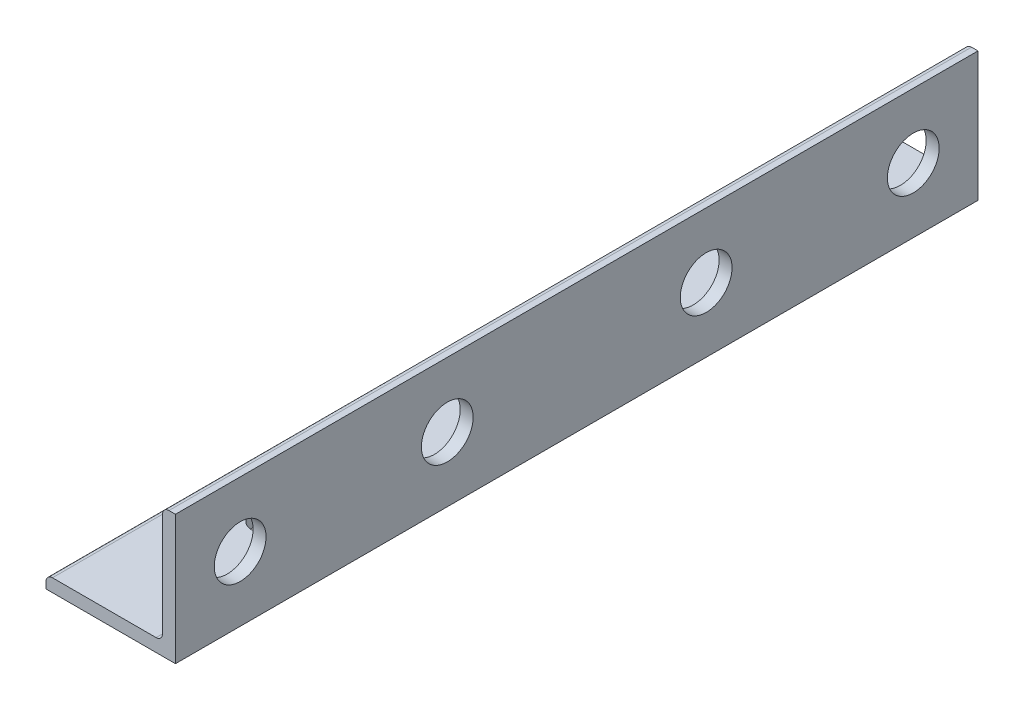
SolidWorks part; units mm, degrees
material "McMaster 6061-T6"
ref_plane "Front Plane" through (0, 0, 0) normal (0, 0, 1) x (1, 0, 0)
ref_plane "Top Plane" through (0, 0, 0) normal (0, 1, 0) x (1, 0, 0)
ref_plane "Right Plane" through (0, 0, 0) normal (1, 0, 0) x (0, 0, -1)
sketch "Sketch2" plane through (0, 0, 0) normal (0, 0, 1) x (1, 0, 0)
  line L0 (-7.9375, 0) -> (7.9375, 0)
  line L1 (7.9375, 0) -> (7.9375, 15.875)
  line L2 (7.9375, 15.875) -> (6.35, 15.875) construction
  line L3 (6.35, 15.0813) -> (6.35, 2.3812)
  line L4 (5.5563, 1.5875) -> (-7.1438, 1.5875)
  line L5 (-7.9375, 0) -> (-7.9375, 1.5875) construction
  line L6 (7.1438, 15.875) -> (7.9375, 15.875)
  line L7 (-7.9375, 0.7937) -> (-7.9375, 0)
  arc A0 (6.35, 15.0813) -> (7.1438, 15.875) centre (7.1438, 15.0813) cw
  arc A1 (-7.9375, 0.7937) -> (-7.1438, 1.5875) centre (-7.1438, 0.7937) cw
  arc A2 (6.35, 2.3812) -> (5.5563, 1.5875) centre (5.5563, 2.3812) cw
  dimension "Vert" = 15.875
  dimension "Horz" = 15.875
  dimension "Thickness" = 1.5875
extrude "Boss-Extrude1" add sketch "Sketch2" along normal mid plane 98.425
ref_plane "Contact Plane 1" through (0, 1.5875, 0) normal (0, 1, 0) x (1, 0, 0)
ref_plane "Contact Plane 2" through (6.35, 0, 0) normal (-1, 0, 0) x (0, 0, 1)
sketch "Sketch3" plane through (7.9375, 0, 0) normal (1, 0, 0) x (0, 0, -1)
  line L0 (41.275, 7.9375) -> (-41.275, 7.9375) construction
  line L1 (-49.2125, 15.875) -> (49.2125, 15.875) construction
  line L2 (-49.2125, 15.875) -> (-49.2125, 0) construction
  line L3 (-49.2125, 0) -> (49.2125, 0) construction
  line L4 (49.2125, 15.875) -> (49.2125, 0) construction
  circle A0 centre (-41.275, 7.9375) radius 3.175
  circle A1 centre (41.275, 7.9375) radius 3.175
  circle A2 centre (-15.875, 7.9375) radius 3.175
  circle A3 centre (15.875, 7.9375) radius 3.175
  point P6 (49.2125, 7.9375)
  point P10 (0, 15.875)
  point P13 (0, 7.9375)
  dimension "D1" = 6.35
  dimension "D2" = 82.55
  dimension "D3" = 25.4
  dimension "D4" = 25.4
extrude "Cut-Extrude1" cut sketch "Sketch3" against normal through all
sketch "Sketch4" plane through (0, 0, 0) normal (0, -1, 0) x (1, 0, 0)
  line L0 (0, 30.1625) -> (0, -30.1625)
  line L1 (-7.9375, -49.2125) -> (7.9375, -49.2125) construction
  line L2 (5.5563, 49.2125) -> (-7.1438, 49.2125) construction
  line L3 (7.9375, 49.2125) -> (7.9375, -49.2125) construction
  line L4 (0, 30.1625) -> (7.9375, 30.1625)
  line L5 (7.9375, 30.1625) -> (0, 30.1625)
  circle A0 centre (0, -30.1625) radius 1.75
  circle A1 centre (0, 30.1625) radius 1.75
  point P4 (0, 0)
  point P9 (0, -49.2125)
  point P14 (7.9375, 0)
  dimension "D1" = 3.5
  dimension "D2" = 19.05
extrude "Cut-Extrude2" cut sketch "Sketch4" against normal through all
